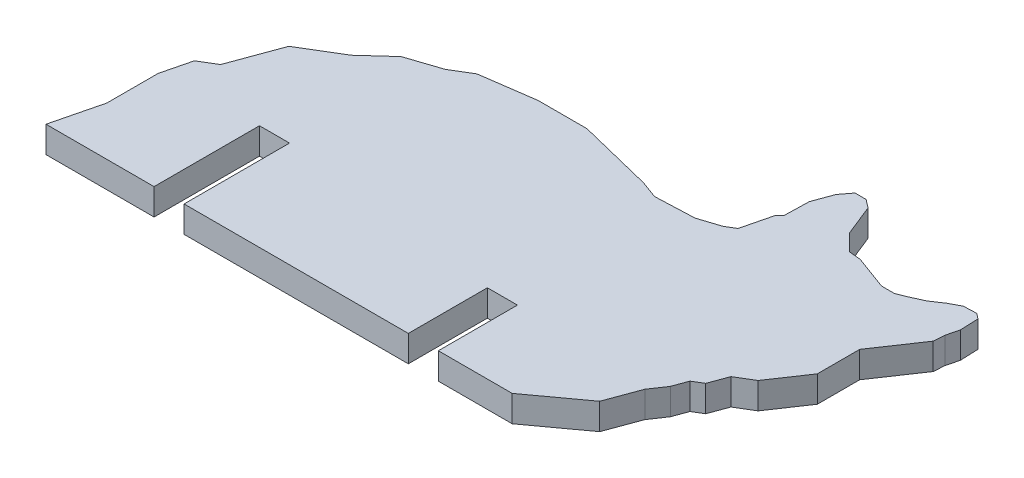
SolidWorks part; units mm, degrees
ref_plane "Front Plane" through (0, 0, 0) normal (0, 0, 1) x (1, 0, 0)
ref_plane "Top Plane" through (0, 0, 0) normal (0, 1, 0) x (1, 0, 0)
ref_plane "Right Plane" through (0, 0, 0) normal (1, 0, 0) x (0, 0, -1)
sketch "Sketch2" plane through (0, 0, 0) normal (0, 1, 0) x (1, 0, 0)
  line L0 (10.1397, 16.6518) -> (50.6983, 16.6518) construction
  line L1 (0, 0) -> (0.5894, 2.3812)
  line L2 (0.5894, 2.3812) -> (1.1449, 4.6252)
  line L3 (1.1449, 4.6252) -> (1.1449, 9.4912)
  line L4 (1.1449, 9.4912) -> (1.8276, 12.2493)
  line L5 (1.8276, 12.2493) -> (3.3777, 13.1843)
  line L6 (3.3777, 13.1843) -> (5.1188, 17.9179)
  line L7 (5.1188, 17.9179) -> (8.8009, 20.1389)
  line L8 (8.8009, 20.1389) -> (11.2808, 22.3946)
  line L9 (11.2808, 22.3946) -> (14.4408, 23.448)
  line L10 (14.4408, 23.448) -> (16.3048, 24.5723)
  line L11 (16.3048, 24.5723) -> (21.3928, 25.2913)
  line L12 (21.3928, 25.2913) -> (26.0275, 25.2913)
  line L13 (26.0275, 25.2913) -> (31.2034, 24.0101)
  line L14 (31.2034, 24.0101) -> (33.157, 23.5266)
  line L15 (33.157, 23.5266) -> (34.8026, 22.9213)
  line L17 (40.5086, 23.7276) -> (41.3851, 24.2563)
  line L18 (41.3851, 24.2563) -> (42.0881, 27.0962)
  line L28 (49.7276, 27.5104) -> (51.6463, 26.8047)
  line L29 (51.6463, 26.8047) -> (52.9229, 26.3352)
  line L39 (59.8947, 24.2563) -> (58.9934, 22.9213)
  line L40 (58.9934, 22.9213) -> (57.8476, 21.224)
  line L41 (57.8476, 21.224) -> (57.0875, 20.0982)
  line L42 (57.0875, 20.0982) -> (57.0875, 16.0746)
  line L43 (57.0875, 16.0746) -> (56.0633, 14.5574)
  line L44 (56.0633, 14.5574) -> (55.7025, 14.0231)
  line L45 (55.7025, 14.0231) -> (55.1363, 13.1843)
  line L46 (55.1363, 13.1843) -> (54.8207, 12.7168)
  line L47 (54.8207, 12.7168) -> (53.2174, 11.7498)
  line L48 (53.2174, 11.7498) -> (52.573, 9.998)
  line L49 (52.573, 9.998) -> (51.6463, 9.439)
  line L50 (51.6463, 9.439) -> (51.1449, 8.0756)
  line L51 (51.1449, 8.0756) -> (50.17, 6.6317)
  line L52 (50.17, 6.6317) -> (49.432, 4.6252)
  line L53 (49.432, 4.6252) -> (49.0194, 3.5032)
  line L54 (49.0194, 3.5032) -> (44.218, 0)
  line L55 (44.218, 0) -> (0, 0)
  line L63 (34.8026, 22.9213) -> (38.5015, 23.0732)
  line L64 (38.5015, 23.0732) -> (40.5086, 23.7276)
  line L65 (42.0881, 27.0962) -> (42.5023, 27.5104)
  line L66 (42.5023, 27.5104) -> (42.564, 29.8475)
  line L81 (42.564, 29.8475) -> (43.2464, 31.7028)
  line L82 (43.2464, 31.7028) -> (44.0237, 32.7195)
  line L83 (44.0237, 32.7195) -> (45.0709, 32.7195)
  line L84 (45.0709, 32.7195) -> (45.8596, 32.1166)
  line L85 (45.8596, 32.1166) -> (46.5078, 30.5032)
  line L86 (46.5078, 30.5032) -> (47.0307, 29.2019)
  line L88 (47.0307, 29.2019) -> (48.2207, 28.012)
  line L89 (48.2207, 28.012) -> (48.6083, 27.6243)
  line L90 (48.6083, 27.6243) -> (49.7276, 27.5104)
  line L91 (52.9229, 26.3352) -> (54.1584, 26.3352)
  line L92 (54.1584, 26.3352) -> (54.9351, 26.6472)
  line L93 (54.9351, 26.6472) -> (56.2827, 27.2521)
  line L94 (56.2827, 27.2521) -> (57.4239, 28.012)
  line L95 (57.4239, 28.012) -> (58.4458, 28.5592)
  line L96 (58.4458, 28.5592) -> (59.6744, 28.6097)
  line L97 (59.6744, 28.6097) -> (60.1941, 28.2124)
  line L98 (60.1941, 28.2124) -> (60.2647, 26.4912)
  line L99 (60.2647, 26.4912) -> (59.9677, 25.2913)
  line L100 (59.9677, 25.2913) -> (59.8947, 24.2563)
extrude "Boss-Extrude4" add sketch "Sketch2" along normal blind 2.5
sketch "Sketch3" plane through (0, 0, 0) normal (0, 0, 1) x (1, 0, 0)
  line L0 (0, 2.5) -> (44.218, 2.5) construction
  line L1 (10.25, 2.5) -> (13.1, 2.5)
  line L2 (10.25, 2.5) -> (10.25, 0)
  line L3 (10.25, 0) -> (13.1, 0)
  line L4 (13.1, 2.5) -> (13.1, 0)
  line L5 (0, 0) -> (44.218, 0) construction
  line L6 (0, 2.5) -> (0, 0) construction
  dimension "D1" = 10.25
  dimension "D2" = 2.85
extrude "Cut-Extrude1" cut sketch "Sketch3" against normal blind 10
sketch "Sketch4" plane through (0, 0, 0) normal (0, 0, 1) x (1, 0, 0)
  line L0 (13.1, 2.5) -> (44.218, 2.5) construction
  line L1 (37.218, 2.5) -> (34.368, 2.5)
  line L2 (37.218, 2.5) -> (37.218, 0)
  line L3 (37.218, 0) -> (34.368, 0)
  line L4 (34.368, 2.5) -> (34.368, 0)
  line L5 (13.1, 0) -> (44.218, 0) construction
  line L6 (44.218, 2.5) -> (44.218, 0) construction
  dimension "D1" = 2.85
  dimension "D2" = 7
extrude "Cut-Extrude2" cut sketch "Sketch4" against normal blind 7.5
